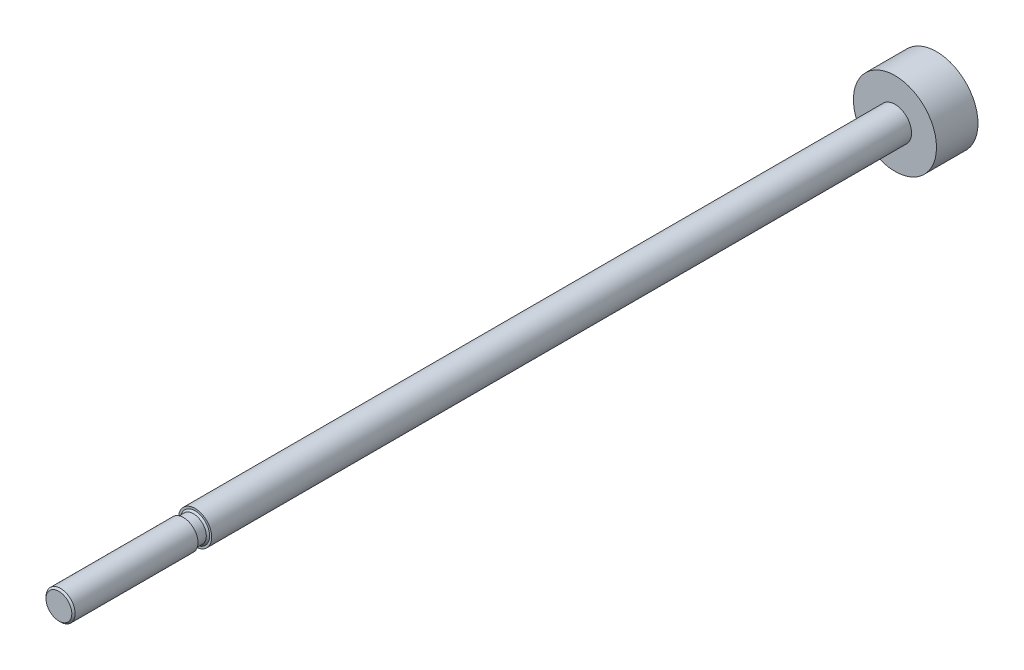
SolidWorks part; units mm, degrees
ref_plane "Front" through (0, 0, 0) normal (0, 0, 1) x (1, 0, 0)
ref_plane "Top" through (0, 0, 0) normal (0, 1, 0) x (1, 0, 0)
ref_plane "Right" through (0, 0, 0) normal (1, 0, 0) x (0, 0, -1)
sketch "Sketch1" plane through (0, 0, 0) normal (0, 0, 1) x (1, 0, 0)
  circle A0 centre (0, 0) radius 2
  dimension "D" = 4
extrude "Base-Extrude" add sketch "Sketch1" along normal up to surface (103.185 mm away)
sketch "Sketch2" plane through (0, 0, 0) normal (0, 0, 1) x (1, 0, 0)
  circle A0 centre (0, 0) radius 5
  dimension "Bore" = 10
extrude "Piston" add sketch "Sketch2" along normal mid plane 5
sketch "Sketch3" plane through (0, 0, 0) normal (1, 0, 0) x (0, 0, -1)
  line L0 (0, 0) -> (-47.8943, 0) construction
  line L1 (-2.5, 0) -> (2.5, 0) construction
  line L2 (-103.185, 1.5525) -> (-102.985, 1.7525)
  line L3 (-103.185, 2) -> (-103.185, -2) construction
  line L4 (-102.985, 1.7525) -> (-88.185, 1.7525)
  line L5 (-88.185, 1.7525) -> (-88.185, 1.55)
  line L6 (-88.185, 1.55) -> (-86.985, 1.55)
  line L8 (-86.985, 1.55) -> (-86.785, 1.75)
  line L10 (-86.785, 1.75) -> (-86.785, 5)
  line L11 (-86.785, 5) -> (-103.185, 5)
  line L12 (-103.185, 5) -> (-103.185, 1.5525)
  line L13 (2.5, 5) -> (-2.5, 5) construction
  dimension "D1" = 0.2
  dimension "D2" = 45
  dimension "D3" = 3.1
  dimension "NN" = 3.505
  dimension "A" = 15
  dimension "D4" = 1.2
revolve "Threads" cut sketch "Sketch3" angle 360 about L0
